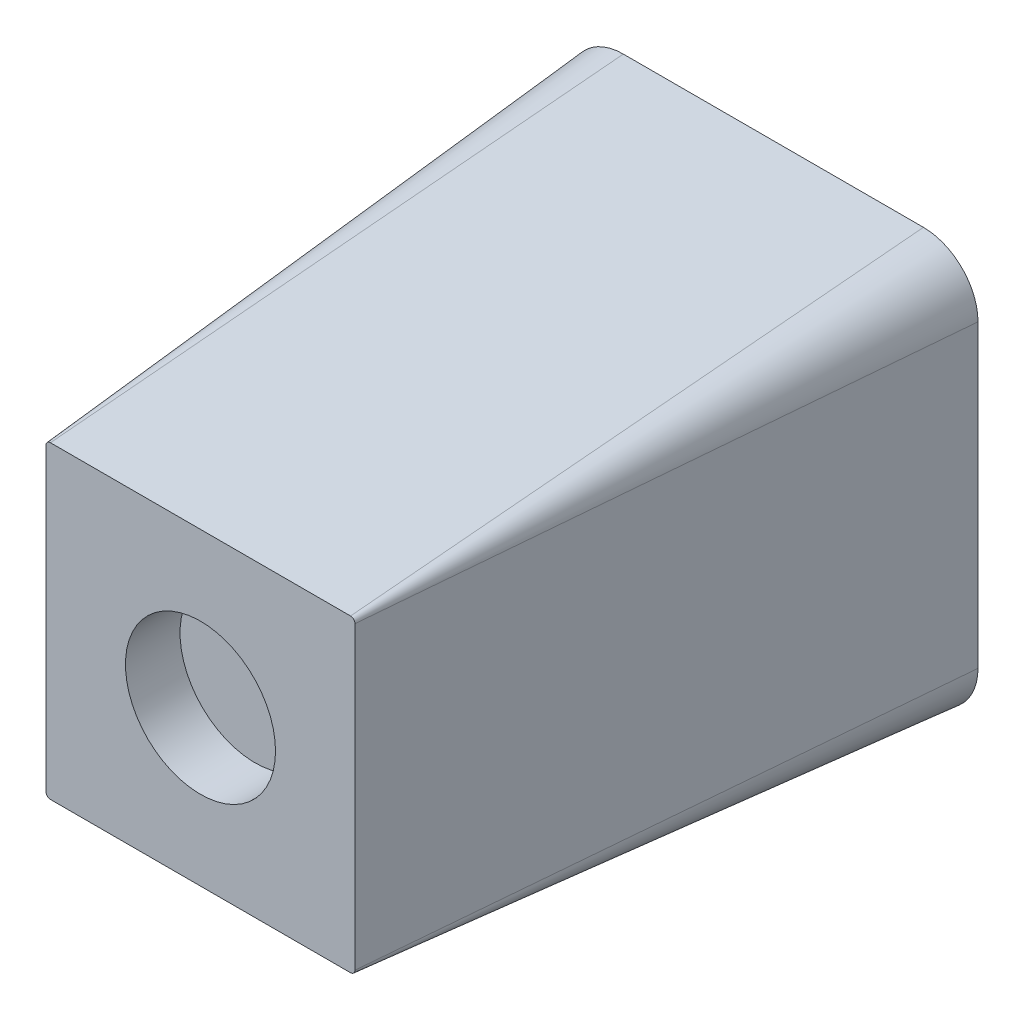
SolidWorks part; units mm, degrees
ref_plane "Спереди" through (0, 0, 0) normal (0, 0, 1) x (1, 0, 0)
ref_plane "Сверху" through (0, 0, 0) normal (0, 1, 0) x (1, 0, 0)
ref_plane "Справа" through (0, 0, 0) normal (1, 0, 0) x (0, 0, -1)
other "Configuration Table"
sketch "Sketch1" plane through (0, 0, 0) normal (0, 0, 1) x (1, 0, 0)
  line L1 (-5.5, -7.5) -> (5.5, -7.5)
  line L2 (-7.5, -5.5) -> (-7.5, 5.5)
  line L3 (-5.5, 7.5) -> (5.5, 7.5)
  line L4 (7.5, -5.5) -> (7.5, 5.5)
  line L5 (-7.5, -7.5) -> (7.5, 7.5) construction
  line L6 (-7.5, 7.5) -> (7.5, -7.5) construction
  arc A0 (-5.5, -7.5) -> (-7.5, -5.5) centre (-5.5, -5.5) cw
  arc A1 (5.5, -7.5) -> (7.5, -5.5) centre (5.5, -5.5) ccw
  arc A2 (5.5, 7.5) -> (7.5, 5.5) centre (5.5, 5.5) cw
  arc A3 (-7.5, 5.5) -> (-5.5, 7.5) centre (-5.5, 5.5) cw
  point P0 (0, 0)
  dimension "D3" = 2
  dimension "D1" = 15
  dimension "D2" = 15
extrude "Boss-Extrude1" add sketch "Sketch1" along normal blind 21 draft 5
sketch "Sketch2" plane through (0, 0, 0) normal (0, 0, -1) x (-1, 0, 0)
  circle A0 centre (0, 0) radius 1.5
  dimension "D1" = 3
extrude "Cut-Extrude1" cut sketch "Sketch2" against normal blind 10
sketch "Sketch3" plane through (0, 0, 21) normal (0, 0, 1) x (1, 0, 0)
  circle A0 centre (0, 0) radius 2.75
  dimension "D1" = 5.5
extrude "Cut-Extrude2" cut sketch "Sketch3" against normal blind 2
